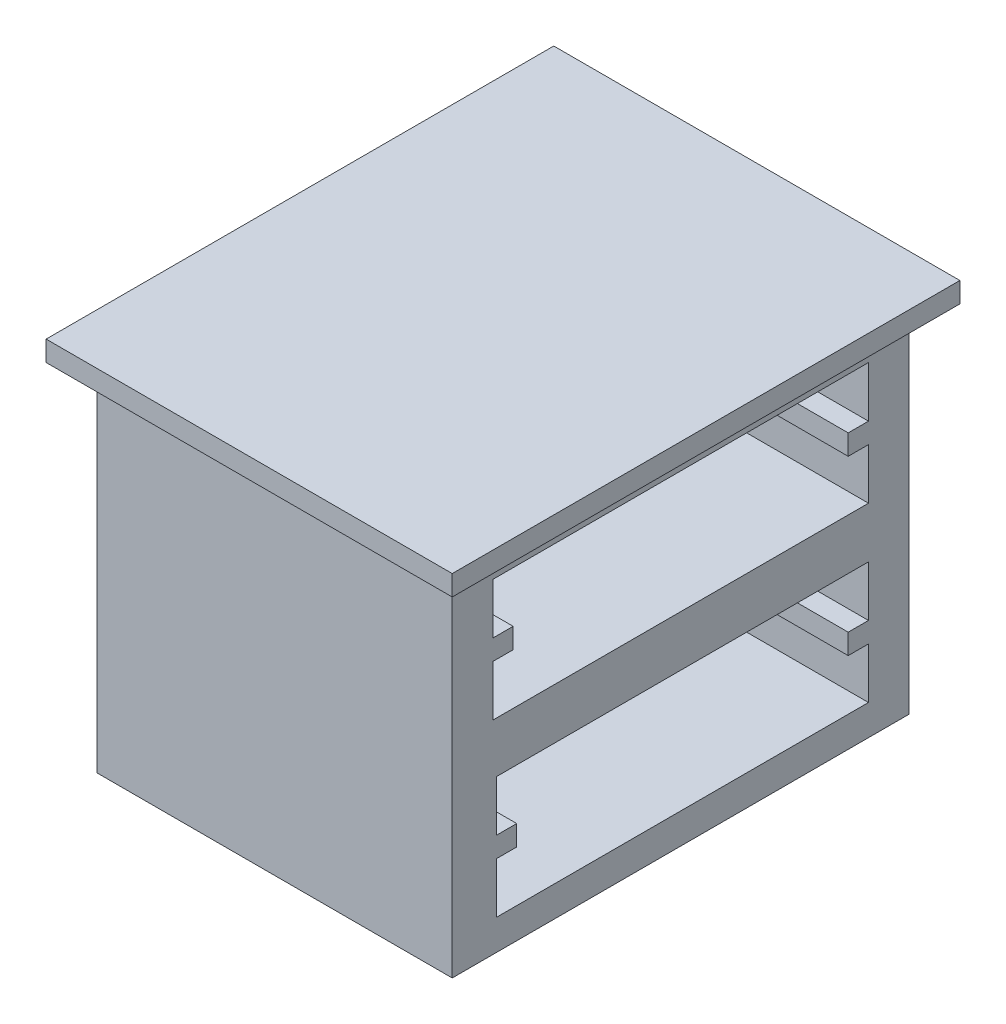
SolidWorks part; units mm, degrees
material "Mahogany"
ref_plane "Front Plane" through (0, 0, 0) normal (0, 0, 1) x (1, 0, 0)
ref_plane "Top Plane" through (0, 0, 0) normal (0, 1, 0) x (1, 0, 0)
ref_plane "Right Plane" through (0, 0, 0) normal (1, 0, 0) x (0, 0, -1)
sketch "Sketch1" plane through (0, 0, 0) normal (0, 1, 0) x (1, 0, 0)
  line L1 (200, -250) -> (-200, -250)
  line L2 (200, -250) -> (200, 250)
  line L3 (200, 250) -> (-200, 250)
  line L4 (-200, -250) -> (-200, 250)
  line L5 (200, -250) -> (-200, 250) construction
  line L6 (200, 250) -> (-200, -250) construction
  point P0 (0, 0)
  dimension "D1" = 500
  dimension "D2" = 400
extrude "Boss-Extrude1" add sketch "Sketch1" against normal blind 20
sketch "Sketch2" plane through (0, -20, 0) normal (0, -1, 0) x (1, 0, 0)
  line L1 (175, 225) -> (-175, 225)
  line L2 (175, 225) -> (175, -225)
  line L3 (175, -225) -> (-175, -225)
  line L4 (-175, 225) -> (-175, -225)
  line L5 (175, 225) -> (-175, -225) construction
  line L6 (175, -225) -> (-175, 225) construction
  point P0 (0, 0)
  dimension "D1" = 450
  dimension "D2" = 350
extrude "Boss-Extrude2" add sketch "Sketch2" along normal blind 350
sketch "Sketch3" plane through (175, 0, 0) normal (1, 0, 0) x (0, 0, -1)
  line L0 (-250, -20) -> (250, -20) construction
  line L1 (-185, -50) -> (185, -50)
  line L2 (-185, -50) -> (-185, -100)
  line L3 (-185, -170) -> (185, -170)
  line L4 (185, -50) -> (185, -100)
  line L5 (-225, -370) -> (-225, -20) construction
  line L6 (225, -370) -> (225, -20) construction
  line L7 (-185, -120) -> (-185, -170)
  line L8 (-185, -100) -> (-165, -100)
  line L10 (-185, -120) -> (-165, -120)
  line L11 (-165, -100) -> (-165, -120)
  line L12 (185, -100) -> (165, -100)
  line L14 (185, -120) -> (165, -120)
  line L15 (165, -100) -> (165, -120)
  line L16 (185, -120) -> (185, -170)
  line L17 (-181.4789, -220) -> (185, -220)
  line L18 (-181.4789, -220) -> (-181.4789, -270)
  line L19 (-181.4789, -340) -> (185, -340)
  line L20 (185, -220) -> (185, -270)
  line L21 (-181.4789, -290) -> (-181.4789, -340)
  line L22 (-181.4789, -270) -> (-161.4789, -270)
  line L23 (-181.4789, -290) -> (-161.4789, -290)
  line L24 (-161.4789, -270) -> (-161.4789, -290)
  line L25 (185, -270) -> (165, -270)
  line L26 (185, -290) -> (165, -290)
  line L27 (165, -270) -> (165, -290)
  line L28 (185, -290) -> (185, -340)
  dimension "D1" = 30
  dimension "D2" = 40
  dimension "D3" = 40
  dimension "D4" = 120
  dimension "D5" = 20
  dimension "D6" = 20
  dimension "D7" = 20
  dimension "D8" = 20
  dimension "D9" = 50
  dimension "D10" = 50
  dimension "D11" = 50
  dimension "D12" = 50
  dimension "D13" = 50
extrude "Cut-Extrude1" cut sketch "Sketch3" against normal blind 320
